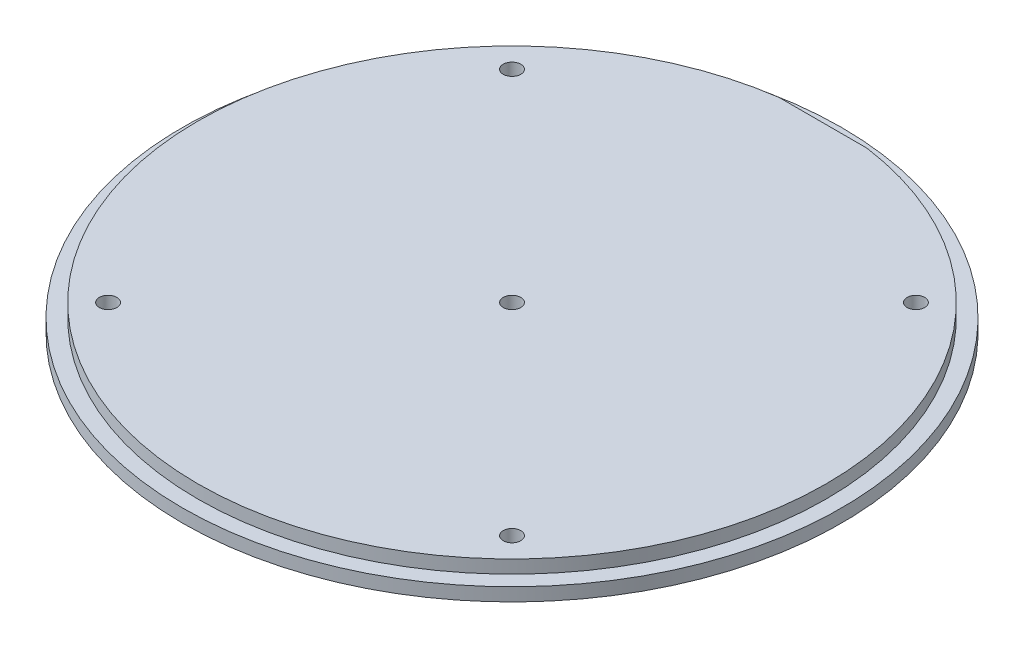
SolidWorks part; units mm, degrees
ref_plane "Front" through (0, 0, 0) normal (0, 0, 1) x (1, 0, 0)
ref_plane "Top" through (0, 0, 0) normal (0, 1, 0) x (1, 0, 0)
ref_plane "Right" through (0, 0, 0) normal (1, 0, 0) x (0, 0, -1)
sketch "Sketch1" plane through (0, 0, 0) normal (0, 1, 0) x (1, 0, 0)
  circle A0 centre (0, 0) radius 75
  dimension "D1" = 150
extrude "Boss-Extrude1" add sketch "Sketch1" along normal blind 3
sketch "Sketch2" plane through (0, 3, 0) normal (0, 1, 0) x (1, 0, 0)
  circle A2 centre (0, 0) radius 71.5
  circle A3 centre (0, 0) radius 71.5
  dimension "D1" = 3.5
extrude "Boss-Extrude2" add sketch "Sketch2" along normal blind 3
sketch "Sketch3" plane through (0, 0, 0) normal (0, -1, 0) x (1, 0, 0)
  line L0 (0, 0) -> (45.9619, 45.9619) construction
  line L1 (50, 0) -> (-50, 0) construction
  circle A0 centre (45.9619, 45.9619) radius 2
  dimension "D1" = 65
  dimension "D2" = 4
  dimension "D3" = 45
extrude "Cut-Extrude1" cut sketch "Sketch3" against normal through all
chamfer "Chamfer1" distance 2 angle 45 1 edges at (45.9619, 0, 43.9619)
pattern_circular "CirPattern1" count 4 over 360 about axis through (0, 0, 0) along (0, 1, 0) of "Cut-Extrude1", "Chamfer1"
sketch "Sketch4" plane through (0, 0, 0) normal (0, -1, 0) x (1, 0, 0)
  circle A0 centre (0, 0) radius 2
  circle A1 centre (45.9619, 45.9619) radius 2 construction
extrude "Cut-Extrude2" cut sketch "Sketch4" against normal through all
chamfer "Chamfer2" distance 2 angle 45 1 edges at (0, 0, -2)
sketch "Sketch5" plane through (0, 6, 0) normal (0, 1, 0) x (1, 0, 0)
  line L0 (-10, 70.7972) -> (10, 70.7972)
  circle A0 centre (0, 0) radius 71.5 construction
  arc A1 (10, 70.7972) -> (-10, 70.7972) centre (0, 0) ccw
  point P5 (0, 70.7972)
  dimension "D1" = 20
extrude "Cut-Extrude4" cut sketch "Sketch5" against normal up to surface (3 mm away) up to face at (0, 3, 71.5)
